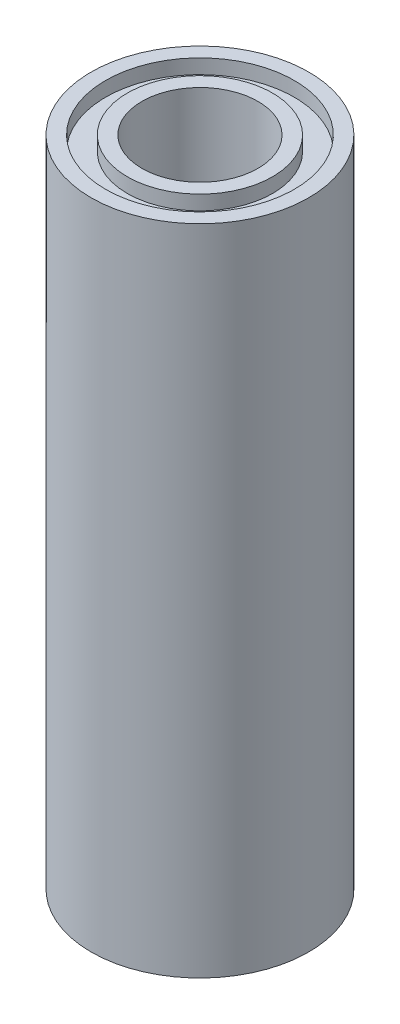
SolidWorks part; units mm, degrees
ref_plane "Front Plane" through (0, 0, 0) normal (0, 0, 1) x (1, 0, 0)
ref_plane "Top Plane" through (0, 0, 0) normal (0, 1, 0) x (1, 0, 0)
ref_plane "Right Plane" through (0, 0, 0) normal (1, 0, 0) x (0, 0, -1)
sketch "Sketch1" plane through (0, 0, 0) normal (0, 1, 0) x (1, 0, 0)
  circle A0 centre (0, 0) radius 7.5
  circle A1 centre (0, 0) radius 4
  dimension "D1" = 8
  dimension "D2" = 15
extrude "Boss-Extrude1" add sketch "Sketch1" along normal blind 45
sketch "Sketch2" plane through (0, 45, 0) normal (0, 1, 0) x (1, 0, 0)
  circle A0 centre (0, 0) radius 6.5
  circle A1 centre (0, 0) radius 5
  circle A2 centre (0, 0) radius 7.5 construction
  dimension "D1" = 10
  dimension "D2" = 13
extrude "Cut-Extrude1" cut sketch "Sketch2" against normal blind 1
